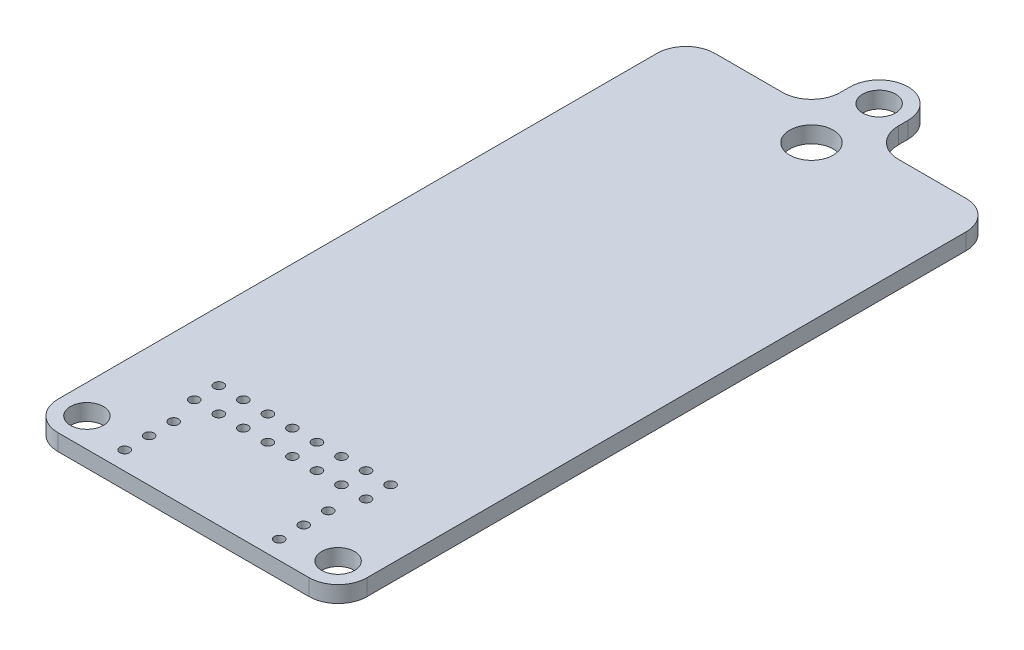
SolidWorks part; units mm, degrees
ref_plane "Front Plane" through (0, 0, 0) normal (0, 0, 1) x (1, 0, 0)
ref_plane "Top Plane" through (0, 0, 0) normal (0, 1, 0) x (1, 0, 0)
ref_plane "Right Plane" through (0, 0, 0) normal (1, 0, 0) x (0, 0, -1)
sketch "Sketch1" plane through (0, 0, 0) normal (0, 1, 0) x (1, 0, 0)
  line L0 (3, 68) -> (10, 68)
  line L1 (3, 0) -> (29, 0)
  line L2 (0, 3) -> (0, 65)
  line L3 (0, 68) -> (32, 68) construction
  line L4 (32, 3) -> (32, 65)
  line L5 (13, 71) -> (13, 72)
  line L6 (19, 72) -> (19, 71)
  line L7 (22, 68) -> (29, 68)
  line L8 (16, 0) -> (16, 144) construction
  line L9 (8.5354, 75) -> (23.2053, 75) construction
  arc A0 (13, 72) -> (19, 72) centre (16, 72) cw
  circle A1 centre (16, 72) radius 1.7
  arc A2 (29, 0) -> (32, 3) centre (29, 3) ccw
  arc A3 (3, 0) -> (0, 3) centre (3, 3) cw
  arc A4 (10, 68) -> (13, 71) centre (10, 71) ccw
  arc A5 (19, 71) -> (22, 68) centre (22, 71) ccw
  arc A6 (29, 68) -> (32, 65) centre (29, 65) cw
  arc A7 (0, 65) -> (3, 68) centre (3, 65) cw
  circle A8 centre (29, 3) radius 1.7
  circle A9 centre (3, 3) radius 1.7
  circle A10 centre (16, 65) radius 2.25
  point P17 (32, 0)
  point P20 (0, 0)
  point P23 (13, 68)
  point P26 (19, 68)
  dimension "D4" = 3.4
  dimension "D6" = 3
  dimension "D7" = 3.4
  dimension "D8" = 4.5
  dimension "D1" = 68
  dimension "D2" = 32
  dimension "D3" = 6
  dimension "D5" = 7
  dimension "D9" = 7
extrude "Boss-Extrude1" add sketch "Sketch1" along normal blind 1.7
sketch "Sketch2" plane through (0, 1.7, 0) normal (0, 1, 0) x (1, 0, 0)
  line L0 (16, 0) -> (16, 75) construction
  line L1 (3, 0) -> (29, 0) construction
  line L2 (0, 65) -> (0, 3) construction
  arc A0 (19, 72) -> (13, 72) centre (16, 72) ccw construction
  circle A1 centre (8, 1.9) radius 0.5
  circle A2 centre (8, 4.44) radius 0.5
  circle A3 centre (8, 6.98) radius 0.5
  circle A4 centre (24, 6.98) radius 0.5
  circle A5 centre (24, 4.44) radius 0.5
  circle A6 centre (24, 1.9) radius 0.5
  circle A7 centre (7.11, 10) radius 0.5
  circle A8 centre (9.65, 10) radius 0.5
  circle A9 centre (12.19, 10) radius 0.5
  circle A10 centre (14.73, 10) radius 0.5
  circle A11 centre (17.27, 10) radius 0.5
  circle A12 centre (19.81, 10) radius 0.5
  circle A13 centre (22.35, 10) radius 0.5
  circle A14 centre (24.89, 10) radius 0.5
  circle A15 centre (9.65, 12.54) radius 0.5
  circle A16 centre (12.19, 12.54) radius 0.5
  circle A17 centre (14.73, 12.54) radius 0.5
  circle A18 centre (17.27, 12.54) radius 0.5
  circle A19 centre (19.81, 12.54) radius 0.5
  circle A20 centre (22.35, 12.54) radius 0.5
  circle A21 centre (24.89, 12.54) radius 0.5
  circle A22 centre (7.11, 12.54) radius 0.5
  dimension "D1" = 1
  dimension "D5" = 1
  dimension "D8" = 10
  dimension "D11" = 2.54
  dimension "D3" = 1.9
  dimension "D4" = 8
  dimension "D9" = 2.54
  dimension "D10" = 2.54
  dimension "D2" = 3
  dimension "D6" = 8
  dimension "D7" = 2
extrude "Cut-Extrude1" cut sketch "Sketch2" against normal up to next
equation "\"mountingHoleDiameter\"= 3.4mm"
equation "\"D4@Sketch1\"=\"mountingHoleDiameter\""
equation "\"D7@Sketch1\"=\"mountingHoleDiameter\""
